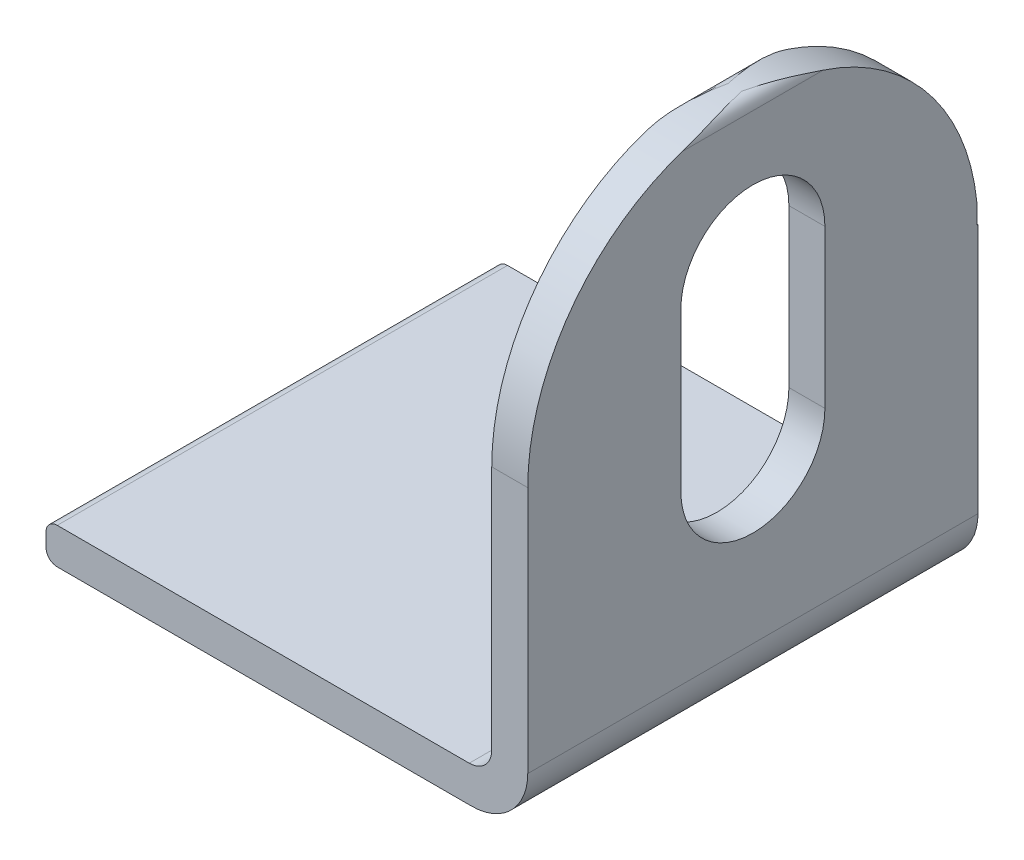
SolidWorks part; units mm, degrees
ref_plane "Front Plane" through (0, 0, 0) normal (0, 0, 1) x (1, 0, 0)
ref_plane "Top Plane" through (0, 0, 0) normal (0, 1, 0) x (1, 0, 0)
ref_plane "Right Plane" through (0, 0, 0) normal (1, 0, 0) x (0, 0, -1)
sketch "Sketch1" plane through (0, 0, 0) normal (0, 0, 1) x (1, 0, 0)
  line L0 (1, 0) -> (37.8, 0)
  line L1 (0, 1) -> (0, 2.2)
  line L2 (1, 3.2) -> (37.6, 3.2)
  line L3 (42.8, 3.2) -> (42.8, 0)
  line L4 (42.8, 5) -> (42.8, 46)
  line L5 (41.8, 47) -> (40.6, 47)
  line L6 (39.6, 46) -> (39.6, 5.2)
  arc A0 (42.8, 5) -> (37.8, 0) centre (37.8, 5) cw
  arc A1 (37.6, 3.2) -> (39.6, 5.2) centre (37.6, 5.2) ccw
  arc A2 (41.8, 47) -> (42.8, 46) centre (41.8, 46) cw
  arc A3 (40.6, 47) -> (39.6, 46) centre (40.6, 46) ccw
  arc A4 (1, 0) -> (0, 1) centre (1, 1) cw
  arc A5 (0, 2.2) -> (1, 3.2) centre (1, 2.2) cw
  point P15 (42.8, 47)
  point P18 (39.6, 47)
  point P21 (0, 0)
  point P24 (0, 3.2)
  dimension "D5" = 5
  dimension "D6" = 2
  dimension "D7" = 1
  dimension "D1" = 3.2
  dimension "D2" = 3.2
  dimension "D3" = 42.8
  dimension "D4" = 47
extrude "Boss-Extrude2" add sketch "Sketch1" against normal blind 40 contours A5 L1 A4 L0 A0 L4 A2 L5 A3 L6 A1 L2
sketch "Sketch3" plane through (39.6, 0, 0) normal (-1, 0, 0) x (0, 0, 1)
  line L0 (-20, 47) -> (-20, 27) construction
  line L2 (-40, 47) -> (0, 47) construction
  line L4 (-20, 47) -> (-39.8687, 47)
  line L5 (-39.8687, 47) -> (-40, 27)
  line L6 (-20, 47) -> (0, 47)
  line L7 (0, 47) -> (0, 27)
  arc A0 (0, 27) -> (-40, 27) centre (-20, 27) ccw
  line M3 (0, 5.2) -> (0, 46)
  line M4 (0, 46) -> (-40, 46)
  dimension "D2" = 40
  dimension "D1" = 20
extrude "Cut-Extrude2" cut sketch "Sketch3" against normal blind 40 contours A0 L5 M4 | A0 L4 L5 M4 | A0 L7 L6 M4 | A0 M3 M4
sketch "Sketch7" plane through (0, 0, -40) normal (0, 0, -1) x (-1, 0, 0)
  line L0 (-39.6, 27.254) -> (-42.8, 27.254)
  line L1 (-39.6, 46) -> (-39.6, 5.2) construction
  line L2 (-42.8, 5) -> (-42.8, 46) construction
  line L3 (-42.8, 27.254) -> (-42.8, 46)
  line L5 (-39.6, 46) -> (-39.6, 27.254)
  line L6 (-41.8, 47) -> (-40.6, 47) construction
  arc A0 (-39.6, 46) -> (-40.6, 47) centre (-40.6, 46) ccw construction
  spline S0 degree 3 poles (-42.8, 46) (-42.8131, 46.794) (-42.0697, 47.045) (-41.408, 46.9927) (-41.0129, 47.0065) (-40.7673, 47.003) (-40.359, 46.9963) (-40.1246, 46.8727) (-39.7818, 46.6329) (-39.5365, 46.2644) (-39.6, 46) knots 0 0 0 0 0.368702 0.509486 0.540771 0.665913 0.70259 0.870866 0.902711 1 1 1 1
extrude "Cut-Extrude3" cut sketch "Sketch7" against normal blind 0.1
sketch "Sketch9" plane through (0, 0, -39.9) normal (0, 0, -1) x (-1, 0, 0)
  line L0 (-44.9292, 41.6705) -> (-35.035, 41.7883)
  line L1 (-35.035, 41.7883) -> (-35.035, 47.8395)
  line L2 (-35.035, 47.8395) -> (-45.3868, 47.7163)
  line L3 (-45.3868, 47.7163) -> (-44.9292, 41.6705)
extrude "Cut-Extrude10" cut sketch "Sketch9" against normal blind 0.5 and the other way blind 0.8
sketch "Sketch10" plane through (39.6, 0, 0) normal (-1, 0, 0) x (0, 0, 1)
  line L2 (-20, 19.9) -> (-20, 33.9) construction
  line L5 (-26.4, 19.9) -> (-26.4, 33.9)
  line L6 (-13.6, 19.9) -> (-13.6, 33.9)
  arc A0 (-26.4, 19.9) -> (-13.6, 19.9) centre (-20, 19.9) ccw
  arc A1 (-13.6, 33.9) -> (-26.4, 33.9) centre (-20, 33.9) ccw
  point P0 (-20, 40.3)
  point P1 (-20, 13.5)
  point P4 (-20, 26.9)
  dimension "D2" = 6.4
  dimension "D3" = 6.4
  dimension "D1" = 6.7
  dimension "D4" = 12.8
  dimension "D5" = 26.8
extrude "Cut-Extrude11" cut sketch "Sketch10" against normal blind 10.5
